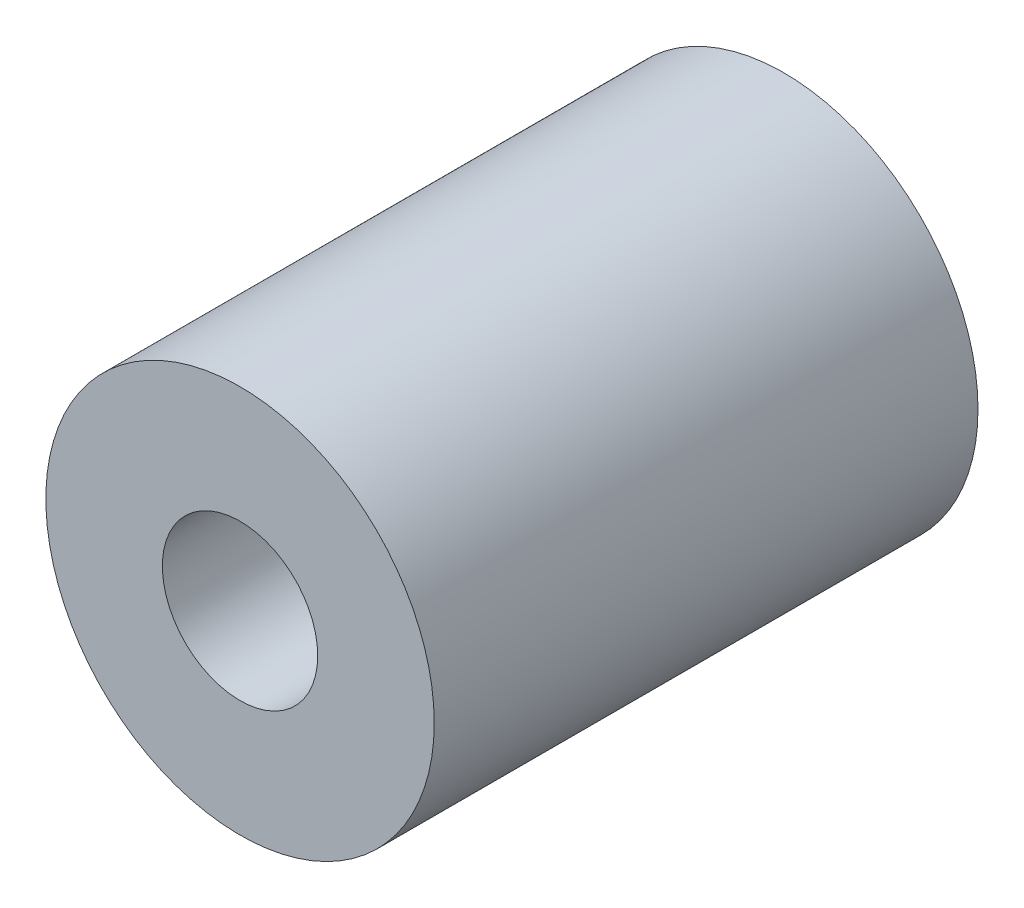
SolidWorks part; units mm, degrees
ref_plane "Front Plane" through (0, 0, 0) normal (0, 0, 1) x (1, 0, 0)
ref_plane "Top Plane" through (0, 0, 0) normal (0, 1, 0) x (1, 0, 0)
ref_plane "Right Plane" through (0, 0, 0) normal (1, 0, 0) x (0, 0, -1)
sketch "Sketch1" plane through (0, 0, 0) normal (0, 0, 1) x (1, 0, 0)
  circle A0 centre (0, 0) radius 5
  dimension "D1" = 10
extrude "Boss-Extrude1" add sketch "Sketch1" along normal blind 14
hole_wizard "Ø4.0mm Dowel Hole1" positions "Sketch2" profile "Sketch3" hole size "Ø4.0" standard "ANSI Metric" end condition up to next
sketch "Sketch2" plane through (0, 0, 14) normal (0, 0, 1) x (1, 0, 0)
  point P0 (0, 0)
sketch "Sketch3" plane through (0, 0, 14) normal (1, 0, 0) x (0, -1, 0)
  line L0 (0, 0) -> (0, 14)
  line L1 (0, 14) -> (2, 14)
  line L2 (2, 14) -> (2, 0)
  line L5 (2, 0) -> (0, 0)
  line L11 (0, -6.35) -> (0, 107.95) construction
  dimension "Thru Hole Dia." = 4
  dimension "Thru Hole Depth" = 14
